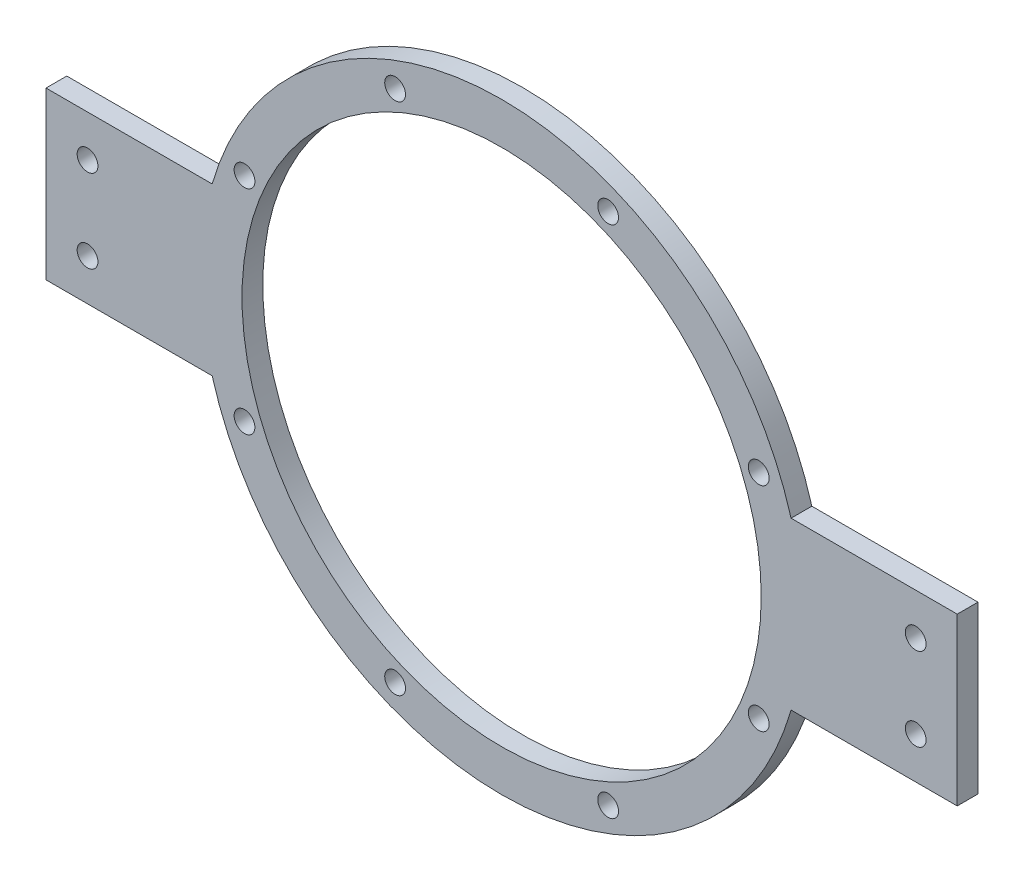
SolidWorks part; units mm, degrees
ref_plane "Front Plane" through (0, 0, 0) normal (0, 0, 1) x (1, 0, 0)
ref_plane "Top Plane" through (0, 0, 0) normal (0, 1, 0) x (1, 0, 0)
ref_plane "Right Plane" through (0, 0, 0) normal (1, 0, 0) x (0, 0, -1)
sketch "Sketch1" plane through (0, 0, 0) normal (0, 0, 1) x (1, 0, 0)
  line L0 (-139.3022, 25.4) -> (-88.5022, 25.4)
  line L1 (-139.3022, -25.4) -> (-88.5022, -25.4)
  line L2 (139.3022, 25.4) -> (88.5022, 25.4)
  line L3 (139.3022, -25.4) -> (88.5022, -25.4)
  line L4 (-139.3022, 25.4) -> (-139.3022, -25.4)
  line L5 (139.3022, 25.4) -> (139.3022, -25.4)
  circle A0 centre (0, 0) radius 79.375
  arc A1 (-88.5022, -25.4) -> (88.5022, -25.4) centre (0, 0) ccw
  arc A2 (88.5022, 25.4) -> (-88.5022, 25.4) centre (0, 0) ccw
  dimension "D1" = 158.75
  dimension "D2" = 92.075
  dimension "D3" = 50.8
  dimension "D4" = 50.8
extrude "Boss-Extrude1" add sketch "Sketch1" along normal blind 6.35 contours A0
sketch "Sketch2" plane through (0, 0, 6.35) normal (0, 0, 1) x (1, 0, 0)
  line L0 (-32.5625, 78.6129) -> (32.5625, -78.6129) construction
  line L1 (-78.6129, 32.5625) -> (-78.6129, -32.5625) construction
  line L2 (-88.5022, 25.4) -> (-139.3022, 25.4) construction
  line L3 (-139.3022, 25.4) -> (-139.3022, -25.4) construction
  line L4 (-139.3022, -25.4) -> (-88.5022, -25.4) construction
  line L5 (139.3022, -25.4) -> (139.3022, 25.4) construction
  line L6 (139.3022, 25.4) -> (88.5022, 25.4) construction
  line L7 (88.5022, -25.4) -> (139.3022, -25.4) construction
  circle A0 centre (-32.5625, 78.6129) radius 3.175
  circle A1 centre (32.5625, 78.6129) radius 3.175
  circle A2 centre (78.6129, 32.5625) radius 3.175
  circle A3 centre (78.6129, -32.5625) radius 3.175
  circle A4 centre (32.5625, -78.6129) radius 3.175
  circle A5 centre (-32.5625, -78.6129) radius 3.175
  circle A6 centre (-78.6129, -32.5625) radius 3.175
  circle A7 centre (-78.6129, 32.5625) radius 3.175
  circle A8 centre (-126.6022, 12.7) radius 3.175
  circle A9 centre (-126.6022, -12.7) radius 3.175
  circle A10 centre (126.6022, 12.7) radius 3.175
  circle A11 centre (126.6022, -12.7) radius 3.175
  point P21 (0, 0)
  dimension "D2" = 6.35
  dimension "D4" = 12.7
  dimension "D5" = 12.7
  dimension "D6" = 12.7
  dimension "D7" = 12.7
  dimension "D8" = 12.7
  dimension "D9" = 12.7
  dimension "D10" = 12.7
  dimension "D11" = 6.35
  dimension "D12" = 12.7
  dimension "D1" = 170.18
  dimension "D3" = 8
extrude "Cut-Extrude1" cut sketch "Sketch2" against normal blind 76.2 contours A9 | A6 | A3 | A10 | A11 | A2 | A1 | A8 | A5 | A4 | A0 | A7
